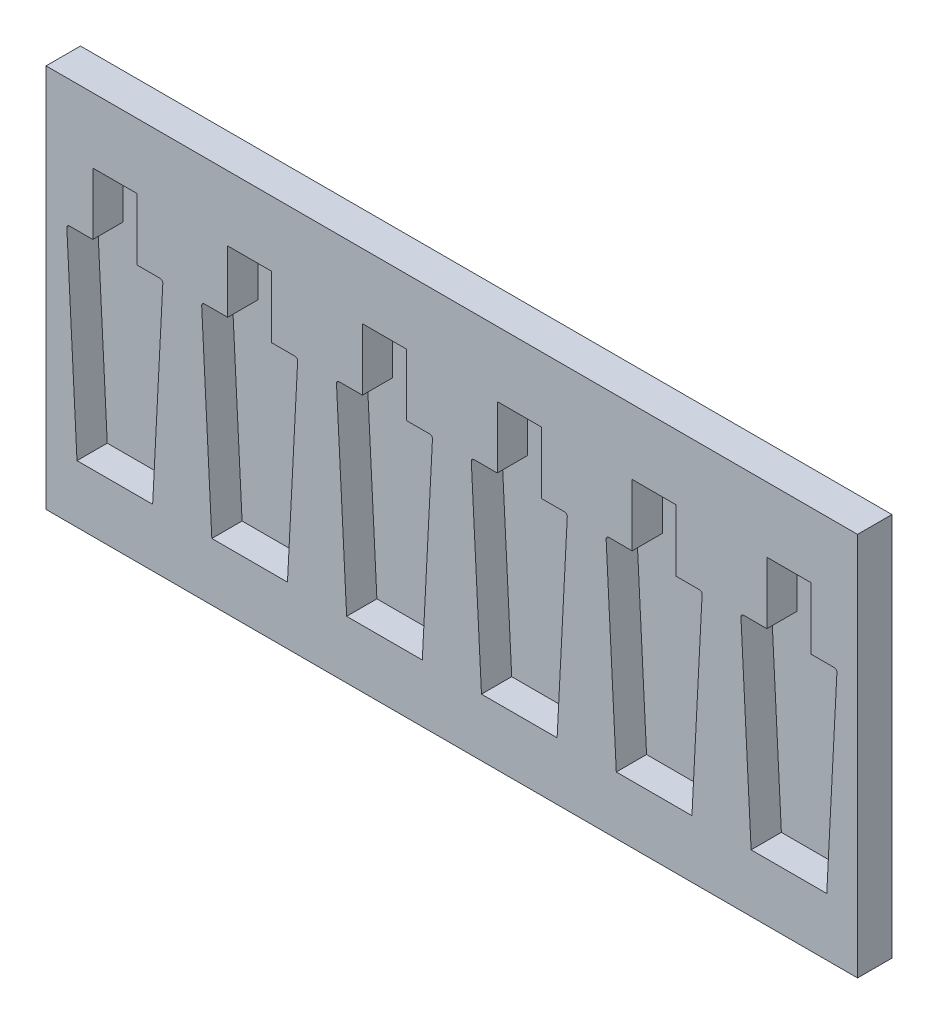
SolidWorks part; units mm, degrees
ref_plane "Front Plane" through (0, 0, 0) normal (0, 0, 1) x (1, 0, 0)
ref_plane "Top Plane" through (0, 0, 0) normal (0, 1, 0) x (1, 0, 0)
ref_plane "Right Plane" through (0, 0, 0) normal (1, 0, 0) x (0, 0, -1)
sketch "Sketch2" plane through (0, 0, 0) normal (0, 0, 1) x (1, 0, 0)
  line L1 (-295, 139.665) -> (295, 139.665)
  line L2 (-295, 139.665) -> (-295, -139.665)
  line L3 (-295, -139.665) -> (295, -139.665)
  line L4 (295, 139.665) -> (295, -139.665)
  line L5 (-295, 139.665) -> (295, -139.665) construction
  line L6 (-295, -139.665) -> (295, 139.665) construction
  point P0 (0, 0)
  dimension "D1" = 590
  dimension "D2" = 279.33
extrude "Boss-Extrude1" add sketch "Sketch2" along normal blind 25
sketch "Sketch3" plane through (0, 0, 0) normal (0, 0, 1) x (1, 0, 0)
  line L0 (-261, 47.335) -> (-261, 92.335)
  line L1 (-261, 92.335) -> (-229, 92.335)
  line L2 (-229, 92.335) -> (-229, 47.335)
  line L3 (-229, 47.335) -> (-212.1061, 47.335)
  line L5 (-217.5, -97.665) -> (-272.5, -97.665)
  line L7 (-277.8939, 47.335) -> (-261, 47.335)
  line L8 (295, -139.665) -> (295, 139.665) construction
  line L9 (-279.8912, 45.2317) -> (-272.5, -97.665)
  line L10 (-210.1088, 45.2317) -> (-217.5, -97.665)
  line L11 (-295, -139.665) -> (295, -139.665) construction
  line L13 (-295, 139.665) -> (-295, -139.665) construction
  line L14 (-112.087, 45.2317) -> (-119.4782, -97.665)
  line L15 (-119.4782, -97.665) -> (-174.4782, -97.665)
  line L16 (-181.8694, 45.2317) -> (-174.4782, -97.665)
  line L17 (-179.8721, 47.335) -> (-162.9782, 47.335)
  line L18 (-162.9782, 47.335) -> (-162.9782, 92.335)
  line L19 (-162.9782, 92.335) -> (-130.9782, 92.335)
  line L20 (-130.9782, 92.335) -> (-130.9782, 47.335)
  line L21 (-130.9782, 47.335) -> (-114.0844, 47.335)
  line L22 (-14.0653, 45.2317) -> (-21.4565, -97.665)
  line L23 (-21.4565, -97.665) -> (-76.4565, -97.665)
  line L24 (-83.8477, 45.2317) -> (-76.4565, -97.665)
  line L25 (-81.8504, 47.335) -> (-64.9565, 47.335)
  line L26 (-64.9565, 47.335) -> (-64.9565, 92.335)
  line L27 (-64.9565, 92.335) -> (-32.9565, 92.335)
  line L28 (-32.9565, 92.335) -> (-32.9565, 47.335)
  line L29 (-32.9565, 47.335) -> (-16.0626, 47.335)
  line L30 (83.9565, 45.2317) -> (76.5653, -97.665)
  line L31 (76.5653, -97.665) -> (21.5653, -97.665)
  line L32 (14.1741, 45.2317) -> (21.5653, -97.665)
  line L33 (16.1714, 47.335) -> (33.0653, 47.335)
  line L34 (33.0653, 47.335) -> (33.0653, 92.335)
  line L35 (33.0653, 92.335) -> (65.0653, 92.335)
  line L36 (65.0653, 92.335) -> (65.0653, 47.335)
  line L37 (65.0653, 47.335) -> (81.9592, 47.335)
  line L38 (181.9782, 45.2317) -> (174.587, -97.665)
  line L39 (174.587, -97.665) -> (119.587, -97.665)
  line L40 (112.1958, 45.2317) -> (119.587, -97.665)
  line L41 (114.1932, 47.335) -> (131.087, 47.335)
  line L42 (131.087, 47.335) -> (131.087, 92.335)
  line L43 (131.087, 92.335) -> (163.087, 92.335)
  line L44 (163.087, 92.335) -> (163.087, 47.335)
  line L45 (163.087, 47.335) -> (179.9809, 47.335)
  line L46 (280, 45.2317) -> (272.6088, -97.665)
  line L47 (272.6088, -97.665) -> (217.6088, -97.665)
  line L48 (210.2176, 45.2317) -> (217.6088, -97.665)
  line L49 (212.2149, 47.335) -> (229.1088, 47.335)
  line L50 (229.1088, 47.335) -> (229.1088, 92.335)
  line L51 (229.1088, 92.335) -> (261.1088, 92.335)
  line L52 (261.1088, 92.335) -> (261.1088, 47.335)
  line L53 (261.1088, 47.335) -> (278.0027, 47.335)
  arc A0 (-212.1061, 47.335) -> (-210.1088, 45.2317) centre (-212.1061, 45.335) cw
  arc A1 (-279.8912, 45.2317) -> (-277.8939, 47.335) centre (-277.8939, 45.335) cw
  arc A2 (-114.0844, 47.335) -> (-112.087, 45.2317) centre (-114.0844, 45.335) cw
  arc A3 (-181.8694, 45.2317) -> (-179.8721, 47.335) centre (-179.8721, 45.335) cw
  arc A4 (-16.0626, 47.335) -> (-14.0653, 45.2317) centre (-16.0626, 45.335) cw
  arc A5 (-83.8477, 45.2317) -> (-81.8504, 47.335) centre (-81.8504, 45.335) cw
  arc A6 (81.9592, 47.335) -> (83.9565, 45.2317) centre (81.9592, 45.335) cw
  arc A7 (14.1741, 45.2317) -> (16.1714, 47.335) centre (16.1714, 45.335) cw
  arc A8 (179.9809, 47.335) -> (181.9782, 45.2317) centre (179.9809, 45.335) cw
  arc A9 (112.1958, 45.2317) -> (114.1932, 47.335) centre (114.1932, 45.335) cw
  arc A10 (278.0027, 47.335) -> (280, 45.2317) centre (278.0027, 45.335) cw
  arc A11 (210.2176, 45.2317) -> (212.2149, 47.335) centre (212.2149, 45.335) cw
  point P2 (0, 0)
  point P9 (-245, 92.335)
  point P10 (-245, -97.665)
  point P16 (-210, 47.335)
  point P19 (-280, 47.335)
  dimension "D9" = 2
  dimension "D1" = 45
  dimension "D2" = 190
  dimension "D3" = 70
  dimension "D4" = 32
  dimension "D5" = 55
  dimension "D6" = 19
  dimension "D7" = 42
  dimension "D8" = 15
  dimension "D11" = 15
  dimension "D10" = 6
sketch "Sketch4" plane through (0, 0, 25) normal (0, 0, 1) x (1, 0, 0)
  line L8 (-261, 47.335) -> (-277.8939, 47.335)
  line L9 (-261, 92.335) -> (-261, 47.335)
  line L10 (-229, 92.335) -> (-261, 92.335)
  line L11 (-229, 47.335) -> (-229, 92.335)
  line L12 (-212.1061, 47.335) -> (-229, 47.335)
  line L13 (-217.5, -97.665) -> (-210.1088, 45.2317)
  line L14 (-272.5, -97.665) -> (-217.5, -97.665)
  line L15 (-279.8912, 45.2317) -> (-272.5, -97.665)
  line L16 (-261, 47.335) -> (-277.8939, 47.335)
  line L17 (-261, 92.335) -> (-261, 47.335)
  line L18 (-229, 92.335) -> (-261, 92.335)
  line L19 (-229, 47.335) -> (-229, 92.335)
  line L20 (-212.1061, 47.335) -> (-229, 47.335)
  line L21 (-217.5, -97.665) -> (-210.1088, 45.2317)
  line L22 (-272.5, -97.665) -> (-217.5, -97.665)
  line L23 (-279.8912, 45.2317) -> (-272.5, -97.665)
  line L24 (-21.4565, -97.665) -> (-14.0653, 45.2317)
  line L25 (-76.4565, -97.665) -> (-21.4565, -97.665)
  line L26 (-83.8477, 45.2317) -> (-76.4565, -97.665)
  line L27 (-64.9565, 47.335) -> (-81.8504, 47.335)
  line L28 (-64.9565, 92.335) -> (-64.9565, 47.335)
  line L29 (-32.9565, 92.335) -> (-64.9565, 92.335)
  line L30 (-32.9565, 47.335) -> (-32.9565, 92.335)
  line L31 (-16.0626, 47.335) -> (-32.9565, 47.335)
  line L32 (-21.4565, -97.665) -> (-14.0653, 45.2317)
  line L33 (-76.4565, -97.665) -> (-21.4565, -97.665)
  line L34 (-83.8477, 45.2317) -> (-76.4565, -97.665)
  line L35 (-64.9565, 47.335) -> (-81.8504, 47.335)
  line L36 (-64.9565, 92.335) -> (-64.9565, 47.335)
  line L37 (-32.9565, 92.335) -> (-64.9565, 92.335)
  line L38 (-32.9565, 47.335) -> (-32.9565, 92.335)
  line L39 (-16.0626, 47.335) -> (-32.9565, 47.335)
  line L40 (-181.8694, 45.2317) -> (-174.4782, -97.665)
  line L41 (-174.4782, -97.665) -> (-119.4782, -97.665)
  line L42 (-119.4782, -97.665) -> (-112.087, 45.2317)
  line L43 (-114.0844, 47.335) -> (-130.9782, 47.335)
  line L44 (-130.9782, 47.335) -> (-130.9782, 92.335)
  line L45 (-130.9782, 92.335) -> (-162.9782, 92.335)
  line L46 (-162.9782, 92.335) -> (-162.9782, 47.335)
  line L47 (-162.9782, 47.335) -> (-179.8721, 47.335)
  line L48 (-181.8694, 45.2317) -> (-174.4782, -97.665)
  line L49 (-174.4782, -97.665) -> (-119.4782, -97.665)
  line L50 (-119.4782, -97.665) -> (-112.087, 45.2317)
  line L51 (-114.0844, 47.335) -> (-130.9782, 47.335)
  line L52 (-130.9782, 47.335) -> (-130.9782, 92.335)
  line L53 (-130.9782, 92.335) -> (-162.9782, 92.335)
  line L54 (-162.9782, 92.335) -> (-162.9782, 47.335)
  line L55 (-162.9782, 47.335) -> (-179.8721, 47.335)
  line L56 (76.5653, -97.665) -> (83.9565, 45.2317)
  line L57 (21.5653, -97.665) -> (76.5653, -97.665)
  line L58 (14.1741, 45.2317) -> (21.5653, -97.665)
  line L59 (33.0653, 47.335) -> (16.1714, 47.335)
  line L60 (33.0653, 92.335) -> (33.0653, 47.335)
  line L61 (65.0653, 92.335) -> (33.0653, 92.335)
  line L62 (65.0653, 47.335) -> (65.0653, 92.335)
  line L63 (81.9592, 47.335) -> (65.0653, 47.335)
  line L64 (76.5653, -97.665) -> (83.9565, 45.2317)
  line L65 (21.5653, -97.665) -> (76.5653, -97.665)
  line L66 (14.1741, 45.2317) -> (21.5653, -97.665)
  line L67 (33.0653, 47.335) -> (16.1714, 47.335)
  line L68 (33.0653, 92.335) -> (33.0653, 47.335)
  line L69 (65.0653, 92.335) -> (33.0653, 92.335)
  line L70 (65.0653, 47.335) -> (65.0653, 92.335)
  line L71 (81.9592, 47.335) -> (65.0653, 47.335)
  line L72 (174.587, -97.665) -> (181.9782, 45.2317)
  line L73 (119.587, -97.665) -> (174.587, -97.665)
  line L74 (112.1958, 45.2317) -> (119.587, -97.665)
  line L75 (131.087, 47.335) -> (114.1932, 47.335)
  line L76 (131.087, 92.335) -> (131.087, 47.335)
  line L77 (163.087, 92.335) -> (131.087, 92.335)
  line L78 (163.087, 47.335) -> (163.087, 92.335)
  line L79 (179.9809, 47.335) -> (163.087, 47.335)
  line L80 (174.587, -97.665) -> (181.9782, 45.2317)
  line L81 (119.587, -97.665) -> (174.587, -97.665)
  line L82 (112.1958, 45.2317) -> (119.587, -97.665)
  line L83 (131.087, 47.335) -> (114.1932, 47.335)
  line L84 (131.087, 92.335) -> (131.087, 47.335)
  line L85 (163.087, 92.335) -> (131.087, 92.335)
  line L86 (163.087, 47.335) -> (163.087, 92.335)
  line L87 (179.9809, 47.335) -> (163.087, 47.335)
  line L88 (210.2176, 45.2317) -> (217.6088, -97.665)
  line L89 (217.6088, -97.665) -> (272.6088, -97.665)
  line L90 (272.6088, -97.665) -> (280, 45.2317)
  line L91 (278.0027, 47.335) -> (261.1088, 47.335)
  line L92 (261.1088, 47.335) -> (261.1088, 92.335)
  line L93 (261.1088, 92.335) -> (229.1088, 92.335)
  line L94 (229.1088, 92.335) -> (229.1088, 47.335)
  line L95 (229.1088, 47.335) -> (212.2149, 47.335)
  line L96 (210.2176, 45.2317) -> (217.6088, -97.665)
  line L97 (217.6088, -97.665) -> (272.6088, -97.665)
  line L98 (272.6088, -97.665) -> (280, 45.2317)
  line L99 (278.0027, 47.335) -> (261.1088, 47.335)
  line L100 (261.1088, 47.335) -> (261.1088, 92.335)
  line L101 (261.1088, 92.335) -> (229.1088, 92.335)
  line L102 (229.1088, 92.335) -> (229.1088, 47.335)
  line L103 (229.1088, 47.335) -> (212.2149, 47.335)
  arc A2 (-210.1088, 45.2317) -> (-212.1061, 47.335) centre (-212.1061, 45.335) ccw
  arc A3 (-277.8939, 47.335) -> (-279.8912, 45.2317) centre (-277.8939, 45.335) ccw
  arc A4 (-210.1088, 45.2317) -> (-212.1061, 47.335) centre (-212.1061, 45.335) ccw
  arc A5 (-277.8939, 47.335) -> (-279.8912, 45.2317) centre (-277.8939, 45.335) ccw
  arc A6 (-81.8504, 47.335) -> (-83.8477, 45.2317) centre (-81.8504, 45.335) ccw
  arc A7 (-14.0653, 45.2317) -> (-16.0626, 47.335) centre (-16.0626, 45.335) ccw
  arc A8 (-81.8504, 47.335) -> (-83.8477, 45.2317) centre (-81.8504, 45.335) ccw
  arc A9 (-14.0653, 45.2317) -> (-16.0626, 47.335) centre (-16.0626, 45.335) ccw
  arc A10 (-179.8721, 47.335) -> (-181.8694, 45.2317) centre (-179.8721, 45.335) ccw
  arc A11 (-112.087, 45.2317) -> (-114.0844, 47.335) centre (-114.0844, 45.335) ccw
  arc A12 (-179.8721, 47.335) -> (-181.8694, 45.2317) centre (-179.8721, 45.335) ccw
  arc A13 (-112.087, 45.2317) -> (-114.0844, 47.335) centre (-114.0844, 45.335) ccw
  arc A14 (16.1714, 47.335) -> (14.1741, 45.2317) centre (16.1714, 45.335) ccw
  arc A15 (83.9565, 45.2317) -> (81.9592, 47.335) centre (81.9592, 45.335) ccw
  arc A16 (16.1714, 47.335) -> (14.1741, 45.2317) centre (16.1714, 45.335) ccw
  arc A17 (83.9565, 45.2317) -> (81.9592, 47.335) centre (81.9592, 45.335) ccw
  arc A18 (114.1932, 47.335) -> (112.1958, 45.2317) centre (114.1932, 45.335) ccw
  arc A19 (181.9782, 45.2317) -> (179.9809, 47.335) centre (179.9809, 45.335) ccw
  arc A20 (114.1932, 47.335) -> (112.1958, 45.2317) centre (114.1932, 45.335) ccw
  arc A21 (181.9782, 45.2317) -> (179.9809, 47.335) centre (179.9809, 45.335) ccw
  arc A22 (212.2149, 47.335) -> (210.2176, 45.2317) centre (212.2149, 45.335) ccw
  arc A23 (280, 45.2317) -> (278.0027, 47.335) centre (278.0027, 45.335) ccw
  arc A24 (212.2149, 47.335) -> (210.2176, 45.2317) centre (212.2149, 45.335) ccw
  arc A25 (280, 45.2317) -> (278.0027, 47.335) centre (278.0027, 45.335) ccw
  dimension "D1" = 0
  dimension "D2" = 0
  dimension "D3" = 0
  dimension "D4" = 0
  dimension "D5" = 0
  dimension "D6" = 0
extrude "Cut-Extrude1" cut sketch "Sketch4" against normal offset from surface (22 mm away) 3 up to face at (0, 0, 0)
